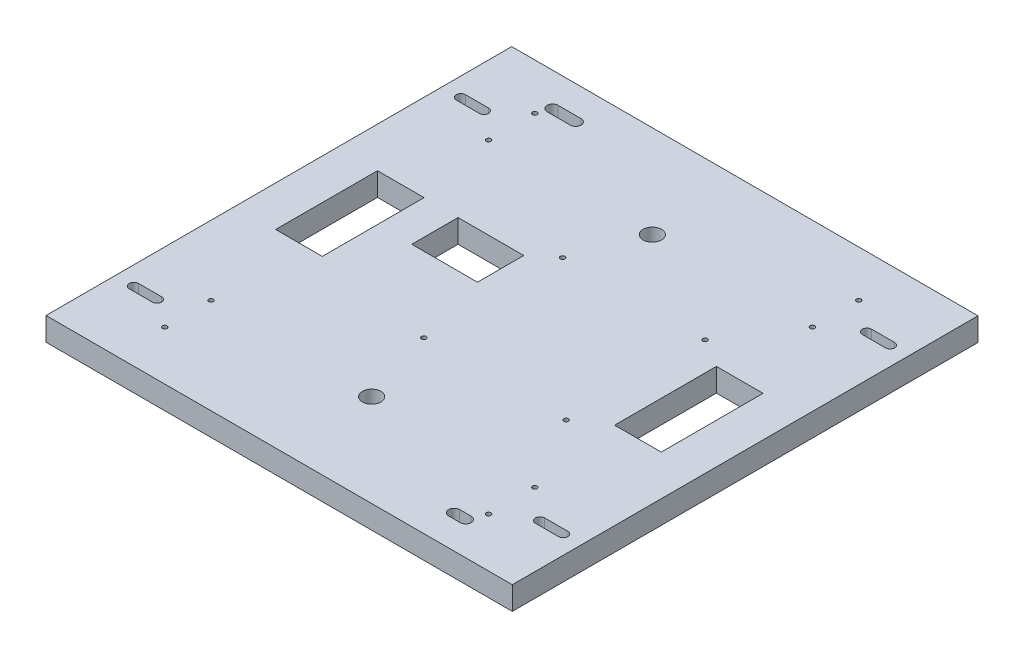
SolidWorks part; units mm, degrees
material "Corrugated Paper"
ref_plane "Front Plane" through (0, 0, 0) normal (0, 0, 1) x (1, 0, 0)
ref_plane "Top Plane" through (0, 0, 0) normal (0, 1, 0) x (1, 0, 0)
ref_plane "Right Plane" through (0, 0, 0) normal (1, 0, 0) x (0, 0, -1)
sketch "Sketch1" plane through (0, 0, 0) normal (0, 1, 0) x (1, 0, 0)
  line L1 (0, 0) -> (127.9906, 0)
  line L2 (0, 0) -> (0, 127.8382)
  line L3 (0, 127.8382) -> (127.9906, 127.8382)
  line L4 (127.9906, 0) -> (127.9906, 127.8382)
  dimension "D1" = 127.9906
  dimension "D2" = 127.8382
extrude "Boss-Extrude1" add sketch "Sketch1" along normal blind 6.35
sketch "Sketch3" plane through (0, 0, 0) normal (0, -1, 0) x (-1, 0, 0)
  line L0 (-5.08, 108.7882) -> (-11.43, 108.7882) construction
  line L1 (-5.08, 107.5182) -> (-11.43, 107.5182)
  line L2 (-5.08, 110.0582) -> (-11.43, 110.0582)
  line L3 (-127.9906, 127.8382) -> (0, 127.8382) construction
  line L5 (0, 127.8382) -> (0, 0) construction
  line L6 (0, 63.9191) -> (-127.9906, 63.9191) construction
  line L7 (-127.9906, 0) -> (-127.9906, 127.8382) construction
  line L8 (-63.9953, 0) -> (-63.9953, 127.8382) construction
  line L9 (0, 0) -> (-127.9906, 0) construction
  line L10 (-122.9106, 108.7882) -> (-116.5606, 108.7882) construction
  line L11 (-122.9106, 107.5182) -> (-116.5606, 107.5182)
  line L12 (-122.9106, 110.0582) -> (-116.5606, 110.0582)
  line L13 (-122.9106, 19.05) -> (-116.5606, 19.05) construction
  line L14 (-122.9106, 20.32) -> (-116.5606, 20.32)
  line L15 (-122.9106, 17.78) -> (-116.5606, 17.78)
  line L16 (-5.08, 19.05) -> (-11.43, 19.05) construction
  line L17 (-5.08, 20.32) -> (-11.43, 20.32)
  line L18 (-5.08, 17.78) -> (-11.43, 17.78)
  line L19 (-20.32, 118.7196) -> (-26.67, 118.7196) construction
  line L20 (-20.32, 117.2083) -> (-26.67, 117.2083)
  line L21 (-20.32, 120.2309) -> (-26.67, 120.2309)
  line L22 (-102.9081, 9.1186) -> (-106.0831, 9.1186) construction
  line L23 (-102.9081, 7.6073) -> (-106.0831, 7.6073)
  line L24 (-102.9081, 10.6299) -> (-106.0831, 10.6299)
  line L25 (-116.9162, 51.9684) -> (-116.9162, 79.9084)
  line L26 (-11.0744, 51.9684) -> (-23.876, 51.9684)
  line L27 (-11.0744, 51.9684) -> (-11.0744, 79.9084)
  line L28 (-11.0744, 79.9084) -> (-23.876, 79.9084)
  line L29 (-23.876, 51.9684) -> (-23.876, 79.9084)
  line L30 (-116.9162, 51.9684) -> (-104.1146, 51.9684)
  line L31 (-104.1146, 51.9684) -> (-104.1146, 79.9084)
  line L32 (-116.9162, 79.9084) -> (-104.1146, 79.9084)
  line L34 (-33.274, 67.1322) -> (-51.308, 67.1322)
  line L35 (-33.274, 67.1322) -> (-33.274, 79.8322)
  line L36 (-33.274, 79.8322) -> (-51.308, 79.8322)
  line L37 (-51.308, 67.1322) -> (-51.308, 79.8322)
  arc A0 (-5.08, 107.5182) -> (-5.08, 110.0582) centre (-5.08, 108.7882) ccw
  arc A1 (-11.43, 110.0582) -> (-11.43, 107.5182) centre (-11.43, 108.7882) ccw
  arc A2 (-122.9106, 107.5182) -> (-122.9106, 110.0582) centre (-122.9106, 108.7882) cw
  arc A3 (-116.5606, 110.0582) -> (-116.5606, 107.5182) centre (-116.5606, 108.7882) cw
  arc A4 (-122.9106, 20.32) -> (-122.9106, 17.78) centre (-122.9106, 19.05) ccw
  arc A5 (-116.5606, 17.78) -> (-116.5606, 20.32) centre (-116.5606, 19.05) ccw
  arc A6 (-5.08, 20.32) -> (-5.08, 17.78) centre (-5.08, 19.05) cw
  arc A7 (-11.43, 17.78) -> (-11.43, 20.32) centre (-11.43, 19.05) cw
  arc A8 (-20.32, 117.2083) -> (-20.32, 120.2309) centre (-20.32, 118.7196) ccw
  arc A9 (-26.67, 120.2309) -> (-26.67, 117.2083) centre (-26.67, 118.7196) ccw
  arc A10 (-102.9081, 7.6073) -> (-102.9081, 10.6299) centre (-102.9081, 9.1186) ccw
  arc A11 (-106.0831, 10.6299) -> (-106.0831, 7.6073) centre (-106.0831, 9.1186) ccw
  circle A12 centre (-63.9953, 25.4) radius 2.54
  circle A13 centre (-63.9953, 102.4382) radius 2.54
  point P2 (-8.255, 108.7882)
  point P21 (-119.7356, 108.7882)
  point P28 (-119.7356, 19.05)
  point P35 (-8.255, 19.05)
  point P42 (-23.495, 118.7196)
  point P49 (-104.4956, 9.1186)
  dimension "D21" = 5.08
  dimension "D1" = 6.35
  dimension "D2" = 19.05
  dimension "D3" = 8.255
  dimension "D4" = 2.54
  dimension "D5" = 6.35
  dimension "D6" = 9.1186
  dimension "D7" = 23.495
  dimension "D8" = 3.0226
  dimension "D9" = 3.175
  dimension "D10" = 23.495
  dimension "D11" = 9.1186
  dimension "D12" = 3.0226
  dimension "D13" = 27.94
  dimension "D14" = 12.8016
  dimension "D15" = 47.9298
  dimension "D16" = 23.876
  dimension "D17" = 12.7
  dimension "D18" = 18.034
  dimension "D19" = 33.274
  dimension "D20" = 48.006
  dimension "D22" = 25.4
extrude "Cut-Extrude1" cut sketch "Sketch3" against normal through all
sketch "Sketch8" plane through (0, -12.7, 0) normal (0, -1, 0) x (1, 0, 0)
  line L0 (0, -127.8382) -> (0, 0) construction
  line L2 (127.9906, -127.8382) -> (0, -127.8382) construction
  circle A0 centre (19.05, -26.2382) radius 0.635
  circle A1 centre (19.05, -13.5382) radius 0.635
  circle A2 centre (19.05, -102.4382) radius 0.635
  circle A3 centre (19.05, -115.1382) radius 0.635
  circle A4 centre (57.15, -84.6582) radius 0.635
  circle A5 centre (57.15, -46.5582) radius 0.635
  circle A6 centre (96.2406, -46.5582) radius 0.635
  circle A7 centre (96.2406, -84.6582) radius 0.635
  circle A8 centre (107.95, -115.1382) radius 0.635
  circle A9 centre (107.95, -102.4382) radius 0.635
  circle A10 centre (107.95, -26.2382) radius 0.635
  circle A11 centre (107.95, -13.5382) radius 0.635
  dimension "D1" = 1.27
  dimension "D3" = 1.27
  dimension "D5" = 1.27
  dimension "D6" = 1.27
  dimension "D13" = 1.27
  dimension "D14" = 1.27
  dimension "D15" = 1.27
  dimension "D21" = 1.27
  dimension "D25" = 1.27
  dimension "D28" = 1.27
  dimension "D31" = 1.27
  dimension "D34" = 1.27
  dimension "D2" = 19.05
  dimension "D4" = 12.7
  dimension "D7" = 19.05
  dimension "D8" = 19.05
  dimension "D9" = 12.7
  dimension "D10" = 12.7
  dimension "D11" = 76.2
  dimension "D12" = 19.05
  dimension "D16" = 38.1
  dimension "D17" = 57.15
  dimension "D18" = 43.18
  dimension "D19" = 57.15
  dimension "D20" = 39.0906
  dimension "D22" = 39.0906
  dimension "D23" = 38.1
  dimension "D24" = 43.18
  dimension "D26" = 12.7
  dimension "D27" = 88.9
  dimension "D29" = 12.7
  dimension "D30" = 88.9
  dimension "D32" = 88.9
  dimension "D33" = 76.2
  dimension "D35" = 12.7
  dimension "D36" = 88.9
extrude "Cut-Extrude2" cut sketch "Sketch8" against normal through all
